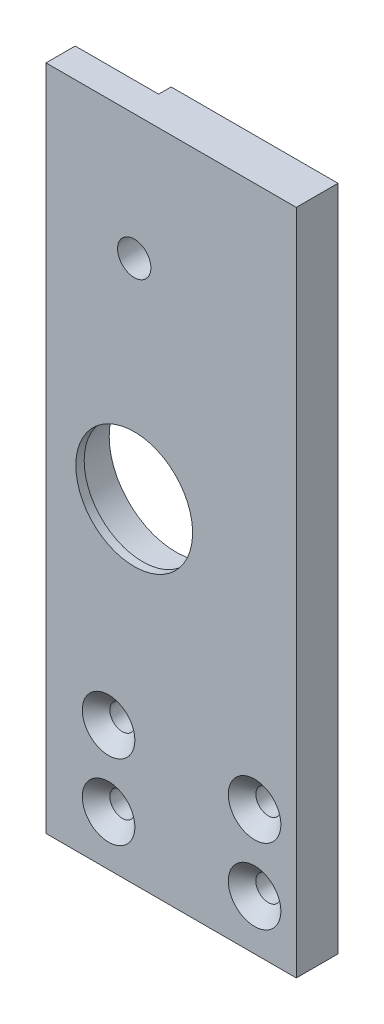
SolidWorks part; units mm, degrees
ref_plane "Ebene vorne" through (0, 0, 0) normal (0, 0, 1) x (1, 0, 0)
ref_plane "Ebene oben" through (0, 0, 0) normal (0, 1, 0) x (1, 0, 0)
ref_plane "Ebene rechts" through (0, 0, 0) normal (1, 0, 0) x (0, 0, -1)
sketch "Skizze1" plane through (0, 0, 0) normal (0, 0, 1) x (1, 0, 0)
  line L1 (0, 0) -> (65, 0)
  line L2 (0, 0) -> (0, 160)
  line L3 (0, 160) -> (65, 160)
  line L4 (65, 0) -> (65, 160)
  dimension "D1" = 160
  dimension "D2" = 65
extrude "Aufsatz-Linear austragen1" add sketch "Skizze1" along normal blind 10
sketch "Skizze2" plane through (0, 0, 0) normal (0, 0, -1) x (-1, 0, 0)
  line L0 (0, 160) -> (0, 0) construction
  line L1 (-65, 160) -> (0, 160) construction
  circle A0 centre (-21.15, 80) radius 16
  dimension "D1" = 32
  dimension "D2" = 21.15
  dimension "D3" = 80
extrude "Schnitt-Linear austragen1" cut sketch "Skizze2" against normal blind 8
sketch "Skizze3" plane through (0, 160, 0) normal (0, 1, 0) x (1, 0, 0)
  line L1 (0, 0) -> (20, 0)
  line L2 (0, 0) -> (0, -3)
  line L3 (0, -3) -> (20, -3)
  line L4 (20, 0) -> (20, -3)
  dimension "D1" = 20
  dimension "D2" = 3
extrude "Schnitt-Linear austragen2" cut sketch "Skizze3" against normal blind 15
sketch "Skizze4" plane through (0, 0, 0) normal (0, 0, -1) x (-1, 0, 0)
  line L0 (0, 145) -> (0, 0) construction
  line L1 (0, 160) -> (-20, 160) construction
  circle A0 centre (-21.15, 130) radius 4
  dimension "D1" = 8
  dimension "D2" = 21.15
  dimension "D3" = 30
extrude "Schnitt-Linear austragen3" cut sketch "Skizze4" against normal blind 20
sketch "Skizze6" plane through (0, 0, 8) normal (0, 0, -1) x (-1, 0, 0)
  line L0 (0, 145) -> (0, 0) construction
  line L2 (0, 160) -> (-20, 160) construction
  circle A0 centre (-21.15, 80) radius 14
  dimension "D2" = 28
  dimension "D1" = 21.15
  dimension "D3" = 80
extrude "Schnitt-Linear austragen4" cut sketch "Skizze6" against normal blind 20
sketch "Skizze7" plane through (0, 0, 3) normal (0, 0, -1) x (-1, 0, 0)
  line L0 (0, 145) -> (0, 160) construction
  line L1 (-20, 145) -> (0, 145) construction
  circle A0 centre (-5, 151) radius 1.62
  dimension "D1" = 3.24
  dimension "D2" = 5
  dimension "D3" = 6
extrude "Schnitt-Linear austragen5" cut sketch "Skizze7" against normal blind 5
cosmetic thread "Gewindedarstellung2" parameters "D1"=5, "D2"=4
sketch "Skizze8" plane through (0, 0, 3) normal (0, 0, -1) x (-1, 0, 0)
  line L0 (-20, 145) -> (0, 145) construction
  line L1 (-20, 145) -> (-20, 160) construction
  circle A0 centre (-15, 151) radius 1.62
  dimension "D1" = 3.24
  dimension "D3" = 5
  dimension "D2" = 6
extrude "Schnitt-Linear austragen6" cut sketch "Skizze8" against normal blind 5
cosmetic thread "Gewindedarstellung1" parameters "D1"=5, "D2"=4
sketch "Skizze9" plane through (0, 0, 10) normal (0, 0, 1) x (1, 0, 0)
  line L0 (0, 0) -> (65, 0) construction
  line L1 (0, 160) -> (0, 0) construction
  circle A0 centre (15, 12) radius 3
  dimension "D1" = 6
  dimension "D2" = 12
  dimension "D3" = 15
extrude "Schnitt-Linear austragen7" cut sketch "Skizze9" against normal blind 32
chamfer "Fase1" distance 3.3 angle 45 1 edges at (18, 12, 10)
sketch "Skizze10" plane through (0, 0, 10) normal (0, 0, 1) x (1, 0, 0)
  line L0 (65, 0) -> (65, 160) construction
  line L1 (0, 0) -> (65, 0) construction
  circle A0 centre (50, 12) radius 3
  dimension "D1" = 6
  dimension "D2" = 15
  dimension "D3" = 12
extrude "Schnitt-Linear austragen8" cut sketch "Skizze10" against normal blind 32
chamfer "Fase2" distance 3.3 angle 45 1 edges at (53, 12, 10)
sketch "Skizze11" plane through (0, 0, 10) normal (0, 0, 1) x (1, 0, 0)
  line L0 (0, 160) -> (0, 0) construction
  line L1 (0, 0) -> (65, 0) construction
  circle A0 centre (15, 30) radius 3
  dimension "D1" = 6
  dimension "D2" = 15
  dimension "D3" = 30
extrude "Schnitt-Linear austragen9" cut sketch "Skizze11" against normal blind 32
chamfer "Fase3" distance 3.3 angle 45 1 edges at (18, 30, 10)
sketch "Skizze12" plane through (0, 0, 10) normal (0, 0, 1) x (1, 0, 0)
  line L0 (65, 0) -> (65, 160) construction
  line L1 (0, 0) -> (65, 0) construction
  circle A0 centre (50, 30) radius 3
  dimension "D1" = 6
  dimension "D2" = 15
  dimension "D3" = 30
extrude "Schnitt-Linear austragen10" cut sketch "Skizze12" against normal blind 25
chamfer "Fase4" distance 3.3 angle 45 1 edges at (53, 30, 10)
sketch "Skizze13" plane through (65, 0, 0) normal (1, 0, 0) x (0, 0, -1)
  line L1 (0, 0) -> (-10, 0)
  line L2 (0, 0) -> (0, 160)
  line L3 (0, 160) -> (-10, 160)
  line L4 (-10, 0) -> (-10, 160)
extrude "Schnitt-Linear austragen11" cut sketch "Skizze13" against normal blind 5
